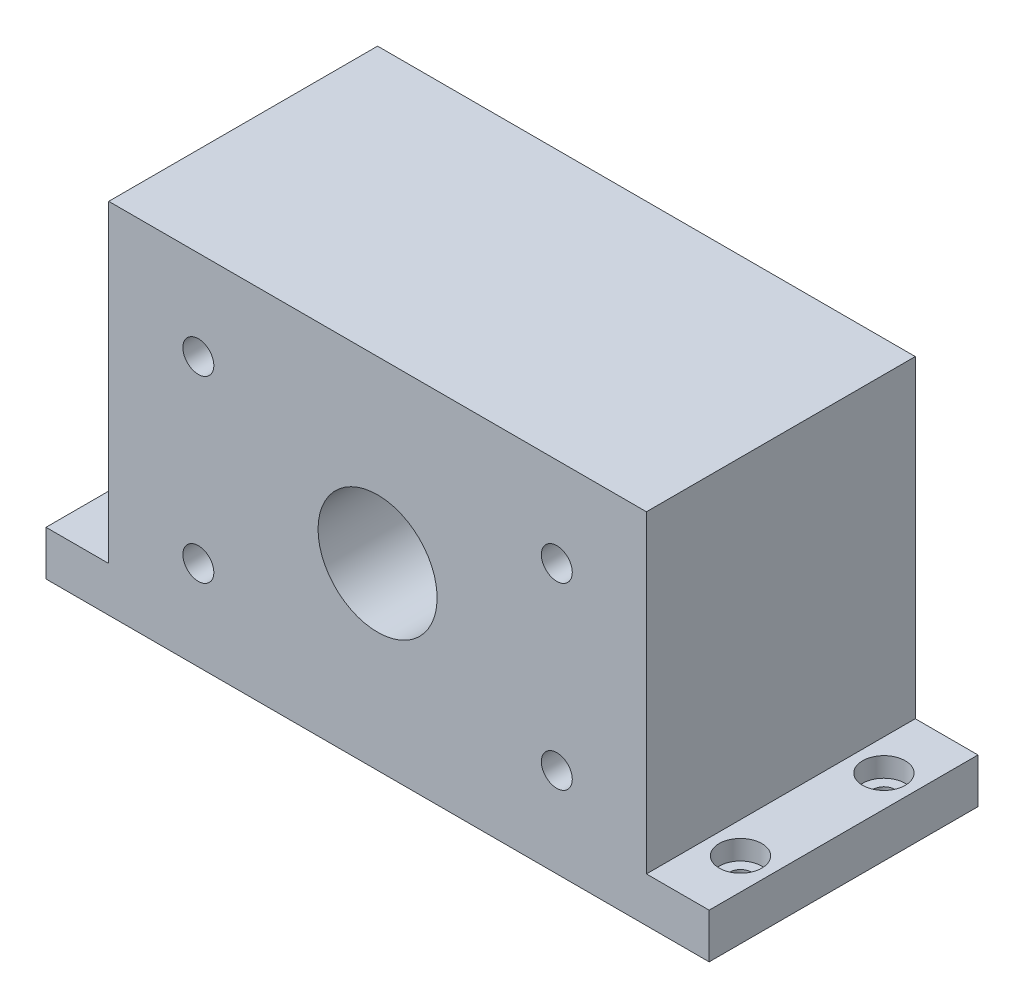
SolidWorks part; units mm, degrees
ref_plane "Front Plane" through (0, 0, 0) normal (0, 0, 1) x (1, 0, 0)
ref_plane "Top Plane" through (0, 0, 0) normal (0, 1, 0) x (1, 0, 0)
ref_plane "Right Plane" through (0, 0, 0) normal (1, 0, 0) x (0, 0, -1)
sketch "Sketch5" plane through (0, 0, 0) normal (0, 1, 0) x (1, 0, 0)
  line L1 (-30, 15) -> (30, 15)
  line L2 (-30, 15) -> (-30, -15)
  line L3 (-30, -15) -> (30, -15)
  line L4 (30, 15) -> (30, -15)
  line L5 (-30, 15) -> (30, -15) construction
  line L6 (-30, -15) -> (30, 15) construction
  point P0 (0, 0)
  dimension "D1" = 30
  dimension "D2" = 60
extrude "Boss-Extrude3" add sketch "Sketch5" along normal blind 40
sketch "Sketch6" plane through (0, 0, 15) normal (0, 0, 1) x (1, 0, 0)
  line L0 (0, 20) -> (-20, 20) construction
  line L3 (-25, 35) -> (25, 35)
  line L4 (-25, 35) -> (-25, 5)
  line L5 (-25, 5) -> (25, 5)
  line L6 (25, 35) -> (25, 5)
  line L7 (-25, 35) -> (25, 5) construction
  line L8 (-25, 5) -> (25, 35) construction
  line L10 (-20, 20) -> (-20, 30) construction
  line L12 (0, 20) -> (20, 20) construction
  line L13 (20, 20) -> (20, 10) construction
  line L14 (-20, 20) -> (-20, 10) construction
  line L15 (20, 20) -> (20, 30) construction
  line L16 (-30, 40) -> (-30, 0) construction
  line L17 (-30, 0) -> (30, 0) construction
  line L18 (-30, 40) -> (30, 40) construction
  point P8 (0, 20)
  dimension "D1" = 50
  dimension "D2" = 30
sketch "Sketch7" plane through (0, 0, -15) normal (0, 0, -1) x (-1, 0, 0)
  line L3 (-20, 10) -> (20, 10)
  line L4 (-20, 10) -> (-20, 30)
  line L5 (-20, 30) -> (20, 30)
  line L6 (20, 10) -> (20, 30)
  line L7 (-20, 10) -> (20, 30) construction
  line L8 (-20, 30) -> (20, 10) construction
  point P8 (0, 20)
  dimension "D1" = 20
  dimension "D2" = 40
extrude "Cut-Extrude1" cut sketch "Sketch7" against normal blind 15
fillet "Fillet1" radius 3 1 edges at (20, 10, -7.5)
fillet "Fillet2" radius 3 1 edges at (-20, 10, -7.5)
fillet "Fillet3" radius 3 1 edges at (-20, 30, -7.5)
fillet "Fillet4" radius 3 1 edges at (20, 30, -7.5)
sketch "Sketch8" plane through (0, 10, 0) normal (0, 1, 0) x (1, 0, 0)
  line L0 (0, 15) -> (0, 0) construction
  line L1 (17, 15) -> (-17, 15) construction
  dimension "D1" = 15
sketch "Sketch9" plane through (-30, 0, 0) normal (-1, 0, 0) x (0, 0, 1)
  line L0 (15, 40) -> (15, 0) construction
  line L1 (-15, 0) -> (15, 0)
  line L2 (-15, 0) -> (-15, 5)
  line L3 (-15, 5) -> (15, 5)
  line L4 (15, 0) -> (15, 5)
extrude "Boss-Extrude4" add sketch "Sketch9" along normal blind 7
sketch "Sketch10" plane through (30, 0, 0) normal (1, 0, 0) x (0, 0, -1)
  line L0 (15, 40) -> (15, 0) construction
  line L1 (-15, 0) -> (15, 0)
  line L2 (-15, 0) -> (-15, 5)
  line L3 (-15, 5) -> (15, 5)
  line L4 (15, 0) -> (15, 5)
extrude "Boss-Extrude5" add sketch "Sketch10" along normal blind 7
sketch "Sketch11" plane through (-30, 0, 0) normal (-1, 0, 0) x (0, 0, 1)
  line L0 (-15, 40) -> (0, 40) construction
  line L1 (-15, 40) -> (15, 40) construction
  line L2 (0, 40) -> (0, 5) construction
  line L3 (15, 5) -> (-15, 5) construction
  line L4 (0, 40) -> (-15, 5) construction
sketch "Sketch12" plane through (-30, 0, 0) normal (-1, 0, 0) x (0, 0, 1)
  circle A0 centre (-7.5315, 22.7105) radius 2
extrude "Cut-Extrude2" cut sketch "Sketch12" against normal blind 10
sketch "Sketch13" plane through (0, 0, 0) normal (0, -1, 0) x (-1, 0, 0)
  line L0 (-37, 15) -> (37, -15) construction
  line L1 (-37, -15) -> (37, 15) construction
  line L3 (-32, 10) -> (32, 10)
  line L4 (-32, 10) -> (-32, -10)
  line L5 (-32, -10) -> (32, -10)
  line L6 (32, 10) -> (32, -10)
  line L7 (-32, 10) -> (32, -10) construction
  line L8 (-32, -10) -> (32, 10) construction
  point P8 (0, 0)
  dimension "D1" = 64
  dimension "D2" = 20
extrude "Cut-Extrude3" cut sketch "Sketch13" against normal blind 1.5
sketch "Sketch14" plane through (0, 0, -15) normal (0, 0, -1) x (-1, 0, 0)
sketch "Sketch16" plane through (0, 5, 0) normal (0, 1, 0) x (1, 0, 0)
  line L3 (37, -15) -> (30, -15) construction
  line L6 (33.5, -15) -> (33.5, -8) construction
  line L7 (33.5004, 14.8485) -> (33.5184, 7.8485) construction
  point P11 (37, -15)
sketch "Sketch18" plane through (0, 5, 0) normal (0, 1, 0) x (1, 0, 0)
  line L2 (-33.5, -15) -> (-33.5, -8) construction
  line L3 (-37, -15) -> (-30, -15) construction
  line L4 (-33.5, 15) -> (-33.5, 8) construction
  line L5 (-37, 15) -> (-30, 15) construction
sketch "Sketch22" plane through (0, 0, -15) normal (0, 0, -1) x (-1, 0, 0)
  line L0 (25, 4) -> (25, 36) construction
  line L1 (-37, 0) -> (37, 0) construction
  line L3 (-30, 40) -> (-30, 0) construction
  line L4 (-25, 20) -> (-25, 36) construction
  line L7 (-25, 20) -> (-25, 4) construction
  line L8 (-25, 36) -> (25, 36) construction
  line L9 (25, 36) -> (25, 4) construction
hole_wizard "#2-56 Tapped Hole2" positions "3DSketch4" profile "Sketch23" tap size "#2-56" standard "ANSI Inch"
sketch3d "3DSketch4"
  point P0 (25, 36, -15)
  point P3 (25, 4, -15)
  point P6 (-25, 4, -15)
sketch "Sketch23" plane through (25, 36, -15) normal (1, 0, 0) x (0, 1, 0)
  line L0 (0, 0) -> (0, 15.5342)
  line L1 (0, 15.5342) -> (0.889, 15)
  line L2 (0.889, 15) -> (0.889, 0)
  line L5 (0.889, 0) -> (0, 0)
  line L10 (0, 15.5342) -> (-0.889, 15) construction
  line L11 (0, -6.35) -> (0, 107.95) construction
  dimension "Tap Drill Dia." = 1.778
  dimension "Tap Drill Depth" = 15
  dimension "Drill Angle" = 118
cosmetic thread "Hole Thread1" parameters "D1"=12, "D2"=2.1844
cosmetic thread "Hole Thread2" parameters "D1"=12, "D2"=2.1844
cosmetic thread "Hole Thread3" parameters "D1"=12, "D2"=2.1844
hole_wizard "#2-56 Tapped Hole3" positions "3DSketch5" profile "Sketch24" tap size "#2-56" standard "ANSI Inch"
sketch3d "3DSketch5"
  point P0 (-25, 36, -15)
sketch "Sketch24" plane through (-25, 36, -15) normal (1, 0, 0) x (0, 1, 0)
  line L0 (0, 0) -> (0, 15.5342)
  line L1 (0, 15.5342) -> (0.889, 15)
  line L2 (0.889, 15) -> (0.889, 0)
  line L5 (0.889, 0) -> (0, 0)
  line L10 (0, 15.5342) -> (-0.889, 15) construction
  line L11 (0, -6.35) -> (0, 107.95) construction
  dimension "Tap Drill Dia." = 1.778
  dimension "Tap Drill Depth" = 15
  dimension "Drill Angle" = 118
cosmetic thread "Hole Thread4" parameters "D1"=12, "D2"=2.1844
hole_wizard "CBORE for #2 Socket Head Cap Screw3" positions "Sketch25" profile "Sketch26" counterbore size "#2" standard "ANSI Inch"
sketch "Sketch25" plane through (0, 5, 0) normal (0, 1, 0) x (1, 0, 0)
  point P0 (-33.5, 8)
  point P3 (-33.5, -8)
sketch "Sketch26" plane through (-33.5, 5, -8) normal (1, 0, 0) x (0, 0, 1)
  line L0 (0, 0) -> (0, 15.7326)
  line L1 (0, 15.7326) -> (1.2192, 15)
  line L2 (1.2192, 15) -> (1.2192, 2.1844)
  line L3 (1.2192, 2.1844) -> (2.3812, 2.1844)
  line L4 (2.3812, 2.1844) -> (2.3812, 0)
  line L5 (2.3812, 0) -> (0, 0)
  line L10 (0, 15.7326) -> (-1.2192, 15) construction
  line L11 (0, -6.35) -> (0, 107.95) construction
  dimension "Hole Dia." = 2.4384
  dimension "Hole Depth" = 15
  dimension "C'Bore Dia." = 4.7625
  dimension "C'Bore Depth" = 2.1844
  dimension "Drill Angle" = 118
hole_wizard "#8-32 Tapped Hole1" positions "Sketch27" profile "Sketch28" tap size "#8-32" standard "ANSI Inch"
sketch "Sketch27" plane through (0, 0, 15) normal (0, 0, 1) x (1, 0, 0)
  point P0 (-20, 30)
  point P3 (-20, 10)
  point P6 (20, 10)
  point P9 (20, 30)
sketch "Sketch28" plane through (-20, 30, 15) normal (1, 0, 0) x (0, -1, 0)
  line L0 (0, 0) -> (0, 12.0378)
  line L1 (0, 12.0378) -> (1.7272, 11)
  line L2 (1.7272, 11) -> (1.7272, 0)
  line L5 (1.7272, 0) -> (0, 0)
  line L10 (0, 12.0378) -> (-1.7272, 11) construction
  line L11 (0, -6.35) -> (0, 107.95) construction
  dimension "Tap Drill Dia." = 3.4544
  dimension "Tap Drill Depth" = 11
  dimension "Drill Angle" = 118
cosmetic thread "Hole Thread5" parameters "D1"=8.33, "D2"=4.1656
cosmetic thread "Hole Thread6" parameters "D1"=8.33, "D2"=4.1656
cosmetic thread "Hole Thread7" parameters "D1"=8.33, "D2"=4.1656
cosmetic thread "Hole Thread8" parameters "D1"=8.33, "D2"=4.1656
sketch "Sketch29" plane through (0, 0, 0) normal (0, 0, -1) x (-1, 0, 0)
  line L0 (-20, 27) -> (-20, 13) construction
sketch "Sketch30" plane through (0, 0, 0) normal (0, 0, -1) x (-1, 0, 0)
  line L0 (20, 27) -> (20, 13) construction
  line L1 (-20, 27) -> (-20, 20) construction
  line L2 (-20, 27) -> (20, 13) construction
  line L3 (-20, 27) -> (-20, 13) construction
  line L4 (0, 20) -> (-12.5, 20) construction
  line L5 (0, 20) -> (12.5, 20) construction
  line L6 (0, 20) -> (-20, 20) construction
  circle A0 centre (-12.5, 20) radius 1.5
  circle A1 centre (12.5, 20) radius 3
sketch "Sketch32" plane through (0, 0, 0) normal (0, 0, -1) x (-1, 0, 0)
  line L0 (0, 10) -> (0, 20) construction
  line L1 (-17, 10) -> (17, 10) construction
  line L2 (25, 35) -> (-25, 5) construction
  line L3 (0, 20) -> (-20, 20) construction
  line L4 (-20, 27) -> (-20, 13) construction
hole_wizard "0.535-40 Tapped Hole1" positions "3DSketch6" profile "Sketch33" tap size "0.535-40" standard "ANSI Inch" end condition through all
sketch3d "3DSketch6"
  point P0 (0, 20, 0)
sketch "Sketch33" plane through (0, 20, 0) normal (1, 0, 0) x (0, 1, 0)
  line L0 (0, 0) -> (0, 15)
  line L1 (0, 15) -> (6.6421, 15)
  line L2 (6.6421, 15) -> (6.6421, 0)
  line L5 (6.6421, 0) -> (0, 0)
  line L11 (0, -6.35) -> (0, 107.95) construction
  dimension "Thru Tap Drill Dia." = 13.2842
  dimension "Thru Tap Drill Depth" = 15
cosmetic thread "Hole Thread9" parameters "D2"=13.589
extrude "Cut-Extrude5" cut sketch "Sketch30" against normal blind 10 contours A0 | A1
sketch "Sketch35" plane through (0, 5, 0) normal (0, 1, 0) x (1, 0, 0)
  line L0 (33.5, -15) -> (33.5, -8) construction
  line L1 (37, -15) -> (30, -15) construction
  line L2 (33.5, 15) -> (33.5, 8) construction
  line L3 (37, 15) -> (30, 15) construction
hole_wizard "CBORE for #2 Socket Head Cap Screw4" positions "3DSketch7" profile "Sketch36" counterbore size "#2" standard "ANSI Inch" end condition through all
sketch3d "3DSketch7"
  point P0 (33.5, 5, 8)
  point P3 (33.5, 5, -8)
sketch "Sketch36" plane through (33.5, 5, 8) normal (1, 0, 0) x (0, 0, 1)
  line L0 (0, 0) -> (0, 5)
  line L1 (0, 5) -> (1.2192, 5)
  line L3 (1.2192, 5) -> (1.2192, 2.1844)
  line L4 (1.2192, 2.1844) -> (2.3812, 2.1844)
  line L5 (2.3812, 2.1844) -> (2.3812, 0)
  line L7 (2.3812, 0) -> (0, 0)
  line L11 (0, -6.35) -> (0, 107.95) construction
  dimension "Thru Hole Dia." = 2.4384
  dimension "Thru Hole Depth" = 5
  dimension "C'Bore Dia." = 4.7625
  dimension "C'Bore Depth" = 2.1844
